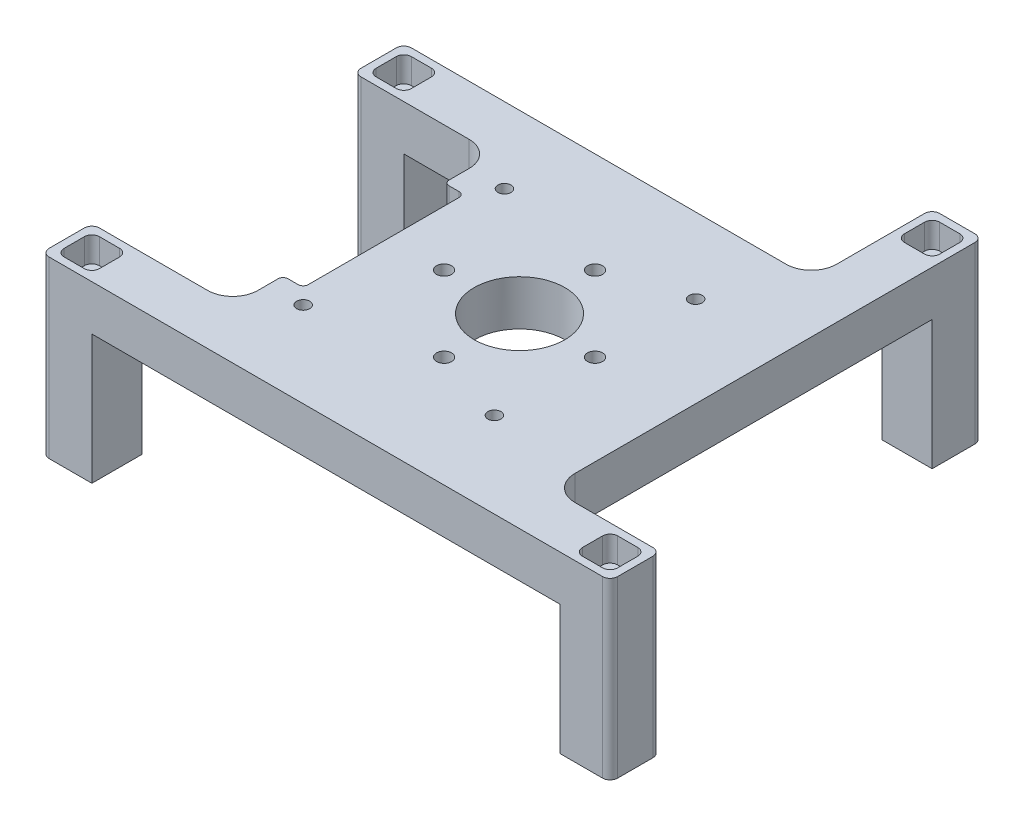
SolidWorks part; units mm, degrees
ref_plane "Front Plane" through (0, 0, 0) normal (0, 0, 1) x (1, 0, 0)
ref_plane "Top Plane" through (0, 0, 0) normal (0, 1, 0) x (1, 0, 0)
ref_plane "Right Plane" through (0, 0, 0) normal (1, 0, 0) x (0, 0, -1)
sketch "Sketch1" plane through (0, 0, 0) normal (0, 1, 0) x (1, 0, 0)
  line L0 (0, 0) -> (66.4625, 0) construction
  line L1 (66.4625, 0) -> (-76.9401, 0) construction
  line L2 (0, 0) -> (0, 53.145) construction
  line L3 (0, 53.145) -> (0, -69.4338) construction
  line L4 (-30, -27) -> (-30, -17)
  line L5 (-30, 25) -> (-58, 25)
  line L6 (-58, 25) -> (-58, 35)
  line L7 (-58, 35) -> (23, 35)
  line L8 (33, 35) -> (33, -27)
  line L9 (33, -37) -> (-26, -37)
  line L10 (23, 35) -> (23, 59)
  line L11 (23, 59) -> (33, 59)
  line L12 (33, 59) -> (33, 35)
  line L13 (-26, -37) -> (-58, -37)
  line L14 (-58, -37) -> (-58, -27)
  line L15 (-58, -27) -> (-30, -27)
  line L16 (33, -27) -> (55, -27)
  line L17 (55, -27) -> (55, -37)
  line L18 (55, -37) -> (33, -37)
  line L19 (-30, -17) -> (-26, -17)
  line L20 (-26, -17) -> (-26, 15)
  line L21 (-26, 15) -> (-30, 15)
  line L22 (-30, 15) -> (-30, 25)
  dimension "D1" = 37
  dimension "D2" = 35
  dimension "D3" = 25
  dimension "D4" = 30
  dimension "D5" = 33
  dimension "D6" = 58
  dimension "D7" = 10
  dimension "D8" = 24
  dimension "D9" = 58
  dimension "D10" = 10
  dimension "D11" = 10
  dimension "D12" = 22
  dimension "D13" = 26
  dimension "D14" = 10
  dimension "D15" = 10
extrude "Boss-Extrude1" add sketch "Sketch1" along normal blind 9
sketch "Sketch2" plane through (0, 9, 0) normal (0, 1, 0) x (1, 0, 0)
  line L0 (0, 0) -> (0, 25.5048) construction
  line L1 (0, 25.5048) -> (0, -33.0557) construction
  line L2 (0, 0) -> (18.4189, 0) construction
  circle A0 centre (0, 0) radius 9
  circle A1 centre (0, 15) radius 1.5
  circle A2 centre (15, 0) radius 1.5
  circle A3 centre (0, -15) radius 1.5
  circle A4 centre (-15, 0) radius 1.5
  point P17 (0, 0)
  dimension "D1" = 18
  dimension "D2" = 3
  dimension "D3" = 0
  dimension "D4" = 15
  dimension "D5" = 4
extrude "Cut-Extrude1" cut sketch "Sketch2" against normal up to next
sketch "Sketch3" plane through (0, 9, 0) normal (0, 1, 0) x (1, 0, 0)
  line L0 (0, 0) -> (0, 42.0355) construction
  line L1 (0, 42.0355) -> (0, -40.4778) construction
  line L2 (0, 0) -> (51.6711, 0) construction
  line L3 (51.6711, 0) -> (-60.4914, 0) construction
  circle A0 centre (-23, 20) radius 1.3
  circle A1 centre (-23, -20) radius 1.3
  circle A2 centre (15, 20) radius 1.3
  circle A3 centre (15, -20) radius 1.3
  dimension "D1" = 2.6
  dimension "D2" = 40
  dimension "D4" = 40
  dimension "D3" = 23
  dimension "D5" = 15
extrude "Cut-Extrude2" cut sketch "Sketch3" against normal up to next
sketch "Sketch4" plane through (0, 0, 0) normal (0, -1, 0) x (1, 0, 0)
  line L0 (-58, -35) -> (-58, -25) construction
  line L1 (-58, -35) -> (-58, -25)
  line L2 (-58, -35) -> (-48, -35)
  line L3 (23, -35) -> (-58, -35) construction
  line L4 (-48, -35) -> (-48, -25)
  line L5 (-58, -25) -> (-30, -25) construction
  line L6 (-48, -25) -> (-58, -25)
extrude "Boss-Extrude2" add sketch "Sketch4" along normal blind 25.7
sketch "Sketch5" plane through (0, 0, 0) normal (0, -1, 0) x (1, 0, 0)
  line L0 (-58, 27) -> (-58, 37) construction
  line L1 (-58, 27) -> (-58, 37)
  line L2 (-58, 37) -> (-48, 37)
  line L3 (-58, 37) -> (55, 37) construction
  line L4 (-48, 37) -> (-48, 27)
  line L5 (-30, 27) -> (-58, 27) construction
  line L6 (-48, 27) -> (-58, 27)
extrude "Boss-Extrude3" add sketch "Sketch5" along normal blind 25.7
sketch "Sketch6" plane through (0, 0, 0) normal (0, -1, 0) x (1, 0, 0)
  line L0 (33, -59) -> (23, -59) construction
  line L1 (33, -59) -> (23, -59)
  line L2 (33, -59) -> (33, -49)
  line L3 (33, 27) -> (33, -59) construction
  line L4 (33, -49) -> (23, -49)
  line L5 (23, -59) -> (23, -35) construction
  line L6 (23, -49) -> (23, -59)
extrude "Boss-Extrude4" add sketch "Sketch6" along normal blind 25.7
sketch "Sketch7" plane through (0, 0, 0) normal (0, -1, 0) x (1, 0, 0)
  line L0 (55, 37) -> (55, 27) construction
  line L1 (55, 37) -> (55, 27)
  line L2 (55, 37) -> (45, 37)
  line L3 (-48, 37) -> (55, 37) construction
  line L4 (45, 37) -> (45, 27)
  line L5 (55, 27) -> (33, 27) construction
  line L6 (45, 27) -> (55, 27)
extrude "Boss-Extrude5" add sketch "Sketch7" along normal blind 25.7
sketch "Sketch8" plane through (0, 9, 0) normal (0, 1, 0) x (1, 0, 0)
  line L0 (55, -37) -> (55, -27) construction
  line L1 (33, 59) -> (23, 59) construction
  line L2 (-58, -27) -> (-58, -37) construction
  line L3 (55, -37) -> (55, -27) construction
  line L4 (33, 59) -> (23, 59) construction
  line L5 (-58, -27) -> (-58, -37) construction
  line L7 (-58, 35) -> (-58, 25) construction
  line L8 (-58, 30) -> (-36.7111, 30) construction
  line L9 (-58, -32) -> (-27.7731, -32) construction
  line L10 (-49.5, 26.5) -> (-56.5, 26.5)
  line L11 (-49.5, 26.5) -> (-49.5, 33.5)
  line L12 (-49.5, 33.5) -> (-56.5, 33.5)
  line L13 (-56.5, 26.5) -> (-56.5, 33.5)
  line L14 (-49.5, 26.5) -> (-56.5, 33.5) construction
  line L15 (-49.5, 33.5) -> (-56.5, 26.5) construction
  line L16 (55, -32) -> (35.3312, -32) construction
  line L17 (-56.5, -35.5) -> (-49.5, -35.5)
  line L18 (-56.5, -35.5) -> (-56.5, -28.5)
  line L19 (-56.5, -28.5) -> (-49.5, -28.5)
  line L20 (-49.5, -35.5) -> (-49.5, -28.5)
  line L21 (-56.5, -35.5) -> (-49.5, -28.5) construction
  line L22 (-56.5, -28.5) -> (-49.5, -35.5) construction
  line L23 (28, 59) -> (28, 34.1932) construction
  line L24 (46.5, -35.5) -> (53.5, -35.5)
  line L25 (46.5, -35.5) -> (46.5, -28.5)
  line L26 (46.5, -28.5) -> (53.5, -28.5)
  line L27 (53.5, -35.5) -> (53.5, -28.5)
  line L28 (46.5, -35.5) -> (53.5, -28.5) construction
  line L29 (46.5, -28.5) -> (53.5, -35.5) construction
  line L31 (24.5, 50.5) -> (31.5, 50.5)
  line L32 (24.5, 50.5) -> (24.5, 57.5)
  line L33 (24.5, 57.5) -> (31.5, 57.5)
  line L34 (31.5, 50.5) -> (31.5, 57.5)
  line L35 (24.5, 50.5) -> (31.5, 57.5) construction
  line L36 (24.5, 57.5) -> (31.5, 50.5) construction
  point P10 (-53, 30)
  point P17 (-53, -32)
  point P24 (50, -32)
  point P31 (28, 54)
  dimension "D1" = 7
  dimension "D2" = 7
  dimension "D3" = 5
  dimension "D4" = 7
  dimension "D5" = 7
  dimension "D6" = 5
  dimension "D7" = 5
  dimension "D8" = 7
  dimension "D9" = 7
  dimension "D10" = 5
  dimension "D11" = 7
  dimension "D12" = 7
extrude "Cut-Extrude3" cut sketch "Sketch8" against normal offset from surface (5 mm away) 5 up to face at (-23, 9, 21.3)
sketch "Sketch9" plane through (0, 4, 0) normal (0, 1, 0) x (1, 0, 0)
  line L0 (-49.5, 26.5) -> (-49.5, 33.5) construction
  line L1 (-56.5, 33.5) -> (-56.5, 26.5) construction
  line L2 (-49.5, 26.5) -> (-49.5, 33.5) construction
  line L3 (-56.5, 33.5) -> (-56.5, 26.5) construction
  line L4 (-56.5, 33.5) -> (-49.5, 26.5) construction
  line L5 (-49.5, 33.5) -> (-56.5, 26.5) construction
  line L6 (31.5, 50.5) -> (31.5, 57.5) construction
  line L7 (24.5, 57.5) -> (24.5, 50.5) construction
  line L8 (31.5, 50.5) -> (31.5, 57.5) construction
  line L9 (24.5, 57.5) -> (24.5, 50.5) construction
  line L12 (24.5, 57.5) -> (31.5, 50.5) construction
  line L13 (31.5, 57.5) -> (24.5, 50.5) construction
  line L14 (53.5, -35.5) -> (53.5, -28.5) construction
  line L15 (46.5, -28.5) -> (46.5, -35.5) construction
  line L16 (-49.5, -35.5) -> (-49.5, -28.5) construction
  line L17 (-56.5, -28.5) -> (-56.5, -35.5) construction
  line L18 (53.5, -35.5) -> (53.5, -28.5) construction
  line L19 (46.5, -28.5) -> (46.5, -35.5) construction
  line L20 (-49.5, -35.5) -> (-49.5, -28.5) construction
  line L21 (-56.5, -28.5) -> (-56.5, -35.5) construction
  line L22 (-56.5, -28.5) -> (-49.5, -35.5) construction
  line L23 (-49.5, -28.5) -> (-56.5, -35.5) construction
  line L24 (46.5, -28.5) -> (53.5, -35.5) construction
  line L25 (53.5, -28.5) -> (46.5, -35.5) construction
  circle A0 centre (-53, 30) radius 1.7
  circle A1 centre (28, 54) radius 1.7
  circle A2 centre (50, -32) radius 1.7
  circle A3 centre (-53, -32) radius 1.7
  dimension "D1" = 3.4
extrude "Cut-Extrude4" cut sketch "Sketch9" against normal up to next
fillet "Fillet1" radius 1.5 24 edges at (53.5, 6.5, 28.5) (53.5, 6.5, 35.5) (46.5, 6.5, 35.5) (46.5, 6.5, 28.5) (55, -8.35, 27) (55, -8.35, 37) (31.5, 6.5, -57.5) (31.5, 6.5, -50.5) (24.5, 6.5, -50.5) (24.5, 6.5, -57.5) (-49.5, 6.5, -26.5) (-56.5, 6.5, -26.5) (-49.5, 6.5, -33.5) (-56.5, 6.5, -33.5) (23, -8.35, -59) (33, -8.35, -59) (-58, -8.35, -25) (-58, -8.35, -35) (-58, -8.35, 27) (-58, -8.35, 37) (-49.5, 6.5, 35.5) (-56.5, 6.5, 35.5) (-49.5, 6.5, 28.5) (-56.5, 6.5, 28.5)
fillet "Fillet2" radius 5 4 edges at (33, 4.5, 27) (-30, 4.5, 27) (23, 4.5, -35) (-30, 4.5, -25)
ref_plane "Plane1" through (0, 6, 0) normal (0, 1, 0) x (1, 0, 0)
sketch "Sketch11" plane through (0, 6, 0) normal (0, 1, 0) x (1, 0, 0)
  line L0 (-23, 23.2909) -> (-29.85, 23.2909)
  line L1 (-20.15, 21.6454) -> (-23, 23.2909)
  line L2 (-23, 23.2909) -> (-25.85, 21.6454) construction
  line L3 (-25.85, 21.6454) -> (-25.85, 18.3546) construction
  line L4 (-25.85, 18.3546) -> (-23, 16.7091) construction
  line L5 (-23, 16.7091) -> (-20.15, 18.3546)
  line L6 (-20.15, 18.3546) -> (-20.15, 21.6454)
  line L7 (17.85, 21.6454) -> (15, 23.2909) construction
  line L8 (15, 23.2909) -> (12.15, 21.6454)
  line L9 (12.15, 21.6454) -> (12.15, 18.3546)
  line L10 (12.15, 18.3546) -> (15, 16.7091)
  line L11 (15, 16.7091) -> (17.85, 18.3546) construction
  line L12 (17.85, 18.3546) -> (17.85, 21.6454) construction
  line L13 (-20.15, -18.3546) -> (-23, -16.7091)
  line L14 (-23, -16.7091) -> (-25.85, -18.3546) construction
  line L15 (-25.85, -18.3546) -> (-25.85, -21.6454) construction
  line L16 (-25.85, -21.6454) -> (-23, -23.2909) construction
  line L17 (-23, -23.2909) -> (-20.15, -21.6454)
  line L18 (-20.15, -21.6454) -> (-20.15, -18.3546)
  line L19 (17.85, -18.3546) -> (15, -16.7091) construction
  line L20 (15, -16.7091) -> (12.15, -18.3546)
  line L21 (12.15, -18.3546) -> (12.15, -21.6454)
  line L22 (12.15, -21.6454) -> (15, -23.2909)
  line L23 (15, -23.2909) -> (17.85, -21.6454) construction
  line L24 (17.85, -21.6454) -> (17.85, -18.3546) construction
  line L25 (-29.85, 23.2909) -> (-29.85, 16.7091)
  line L26 (-29.85, 16.7091) -> (-23, 16.7091)
  line L27 (15, 23.2909) -> (37.85, 23.2909)
  line L28 (37.85, 23.2909) -> (37.85, 16.7091)
  line L29 (37.85, 16.7091) -> (15, 16.7091)
  line L30 (-23, -16.7091) -> (-29.85, -16.7091)
  line L31 (-29.85, -16.7091) -> (-29.85, -23.2909)
  line L32 (-29.85, -23.2909) -> (-23, -23.2909)
  line L33 (15, -16.7091) -> (37.85, -16.7091)
  line L34 (37.85, -16.7091) -> (37.85, -23.2909)
  line L35 (37.85, -23.2909) -> (15, -23.2909)
  circle A0 centre (-23, -20) radius 1.3 construction
  circle A1 centre (15, -20) radius 1.3 construction
  circle A2 centre (15, 20) radius 1.3 construction
  circle A3 centre (-23, -20) radius 1.3 construction
  circle A4 centre (15, -20) radius 1.3 construction
  circle A5 centre (15, 20) radius 1.3 construction
  circle A6 centre (-23, 20) radius 1.3 construction
  circle A7 centre (-23, 20) radius 1.3 construction
  circle A8 centre (-23, 20) radius 2.85 construction
  circle A9 centre (15, 20) radius 2.85 construction
  circle A10 centre (-23, -20) radius 2.85 construction
  circle A11 centre (15, -20) radius 2.85 construction
  dimension "D1" = 5.7
  dimension "D2" = 5.7
  dimension "D3" = 5.7
  dimension "D4" = 5.7
  dimension "D5" = 4
  dimension "D6" = 20
  dimension "D7" = 4
  dimension "D8" = 20
extrude "Cut-Extrude6" [suppressed] cut sketch "Sketch11" against normal blind 2.6
sketch "Sketch12" plane through (0, 0, 0) normal (0, -1, 0) x (1, 0, 0)
  line L1 (-19.9, 18.2102) -> (-19.9, 21.7898)
  line L2 (-19.9, 21.7898) -> (-23, 23.5796)
  line L3 (-23, 23.5796) -> (-26.1, 21.7898)
  line L4 (-26.1, 21.7898) -> (-26.1, 18.2102)
  line L5 (-26.1, 18.2102) -> (-23, 16.4204)
  line L6 (-23, 16.4204) -> (-19.9, 18.2102)
  line L7 (18.1, 21.7898) -> (15, 23.5796)
  line L8 (15, 23.5796) -> (11.9, 21.7898)
  line L9 (11.9, 21.7898) -> (11.9, 18.2102)
  line L10 (11.9, 18.2102) -> (15, 16.4204)
  line L11 (15, 16.4204) -> (18.1, 18.2102)
  line L12 (18.1, 18.2102) -> (18.1, 21.7898)
  line L13 (18.1, -18.2102) -> (15, -16.4204)
  line L14 (15, -16.4204) -> (11.9, -18.2102)
  line L15 (11.9, -18.2102) -> (11.9, -21.7898)
  line L16 (11.9, -21.7898) -> (15, -23.5796)
  line L17 (15, -23.5796) -> (18.1, -21.7898)
  line L18 (18.1, -21.7898) -> (18.1, -18.2102)
  line L19 (-19.9, -18.2102) -> (-23, -16.4204)
  line L20 (-23, -16.4204) -> (-26.1, -18.2102)
  line L21 (-26.1, -18.2102) -> (-26.1, -21.7898)
  line L22 (-26.1, -21.7898) -> (-23, -23.5796)
  line L23 (-23, -23.5796) -> (-19.9, -21.7898)
  line L24 (-19.9, -21.7898) -> (-19.9, -18.2102)
  circle A0 centre (-23, -20) radius 1.3 construction
  circle A1 centre (15, -20) radius 1.3 construction
  circle A2 centre (15, 20) radius 1.3 construction
  circle A3 centre (-23, 20) radius 1.3 construction
  circle A4 centre (-23, -20) radius 1.3 construction
  circle A5 centre (15, -20) radius 1.3 construction
  circle A6 centre (15, 20) radius 1.3 construction
  circle A7 centre (-23, 20) radius 1.3 construction
  circle A8 centre (-23, 20) radius 3.1 construction
  circle A9 centre (15, 20) radius 3.1 construction
  circle A10 centre (15, -20) radius 3.1 construction
  circle A11 centre (-23, -20) radius 3.1 construction
  dimension "D1" = 6.2
  dimension "D2" = 6.2
  dimension "D3" = 6.2
  dimension "D4" = 6.2
extrude "Cut-Extrude7" cut sketch "Sketch12" against normal blind 3
fillet "Fillet3" radius 1 4 edges at (-30, 4.5, -15) (-26, 4.5, -15) (-26, 4.5, 17) (-30, 4.5, 17)
